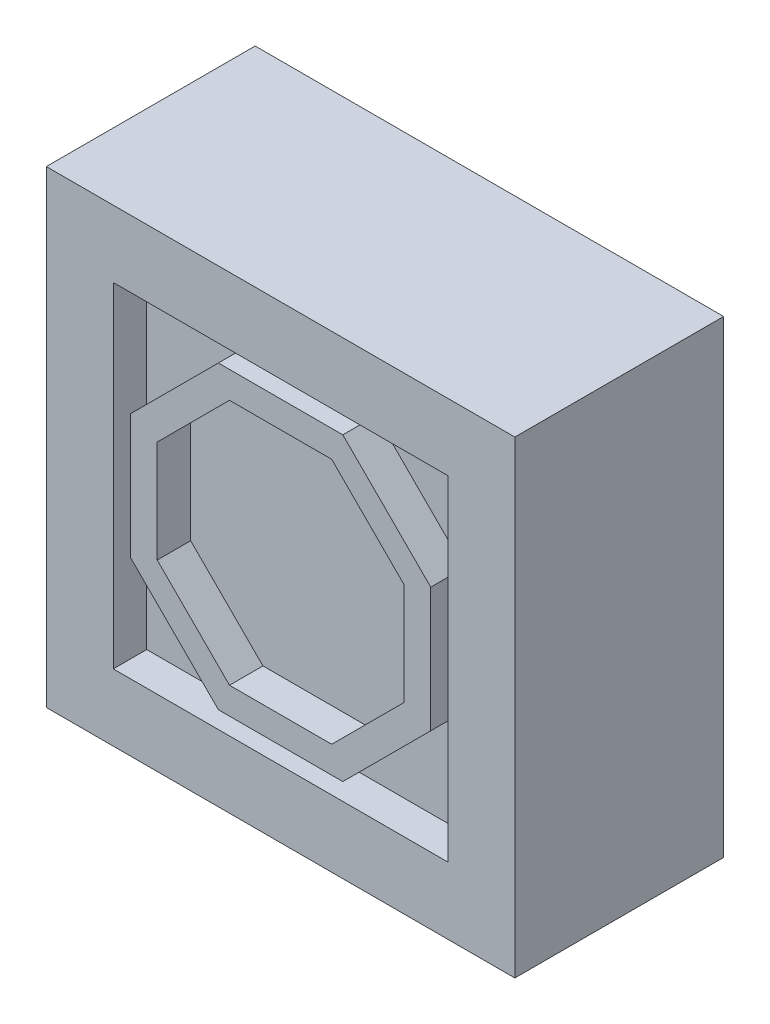
SolidWorks part; units mm, degrees
ref_plane "Front Plane" through (0, 0, 0) normal (0, 0, 1) x (1, 0, 0)
ref_plane "Top Plane" through (0, 0, 0) normal (0, 1, 0) x (1, 0, 0)
ref_plane "Right Plane" through (0, 0, 0) normal (1, 0, 0) x (0, 0, -1)
sketch "Sketch1" plane through (0, 0, 0) normal (0, 0, 1) x (1, 0, 0)
  line L1 (1.75, 1.75) -> (-1.75, 1.75)
  line L2 (1.75, 1.75) -> (1.75, -1.75)
  line L3 (1.75, -1.75) -> (-1.75, -1.75)
  line L4 (-1.75, 1.75) -> (-1.75, -1.75)
  line L5 (1.75, 1.75) -> (-1.75, -1.75) construction
  line L6 (1.75, -1.75) -> (-1.75, 1.75) construction
  point P0 (0, 0)
  dimension "D1" = 3.5
extrude "Boss-Extrude1" add sketch "Sketch1" along normal blind 1.56
sketch "Sketch2" plane through (0, 0, 1.56) normal (0, 0, 1) x (1, 0, 0)
  line L8 (-1.25, 1.25) -> (-1.25, -1.25)
  line L9 (-1.25, -1.25) -> (1.25, -1.25)
  line L10 (1.25, -1.25) -> (1.25, 1.25)
  line L11 (1.25, 1.25) -> (-1.25, 1.25)
  line L12 (-1.25, 1.25) -> (-1.25, -1.25)
  line L13 (-1.25, -1.25) -> (1.25, -1.25)
  line L14 (1.25, -1.25) -> (1.25, 1.25)
  line L15 (1.25, 1.25) -> (-1.25, 1.25)
  dimension "D1" = 0.5
extrude "Cut-Extrude1" cut sketch "Sketch2" against normal blind 0.25
sketch "Sketch3" plane through (0, 0, 1.56) normal (0, 0, 1) x (1, 0, 0)
  line L8 (1.25, 1.25) -> (-1.25, 1.25) construction
  line L9 (-0.4647, 1.1218) -> (-1.1218, 0.4647)
  line L10 (-1.1218, 0.4647) -> (-1.1218, -0.4647)
  line L11 (-1.1218, -0.4647) -> (-0.4647, -1.1218)
  line L12 (-0.4647, -1.1218) -> (0.4647, -1.1218)
  line L13 (0.4647, -1.1218) -> (1.1218, -0.4647)
  line L14 (1.1218, -0.4647) -> (1.1218, 0.4647)
  line L15 (1.1218, 0.4647) -> (0.4647, 1.1218)
  line L16 (0.4647, 1.1218) -> (-0.4647, 1.1218)
  line L17 (-0.3818, 0.9218) -> (-0.9218, 0.3818)
  line L18 (-0.9218, 0.3818) -> (-0.9218, -0.3818)
  line L19 (-0.9218, -0.3818) -> (-0.3818, -0.9218)
  line L20 (-0.3818, -0.9218) -> (0.3818, -0.9218)
  line L21 (0.3818, -0.9218) -> (0.9218, -0.3818)
  line L22 (0.9218, -0.3818) -> (0.9218, 0.3818)
  line L23 (0.9218, 0.3818) -> (0.3818, 0.9218)
  line L24 (0.3818, 0.9218) -> (-0.3818, 0.9218)
  circle A0 centre (0, 0) radius 1.1218 construction
  point P13 (-0.4647, 1.1218)
  dimension "D1" = 0.2
extrude "Boss-Extrude2" add sketch "Sketch3" against normal up to surface (0.25 mm away) up to face at (0, 0, 1.31)
